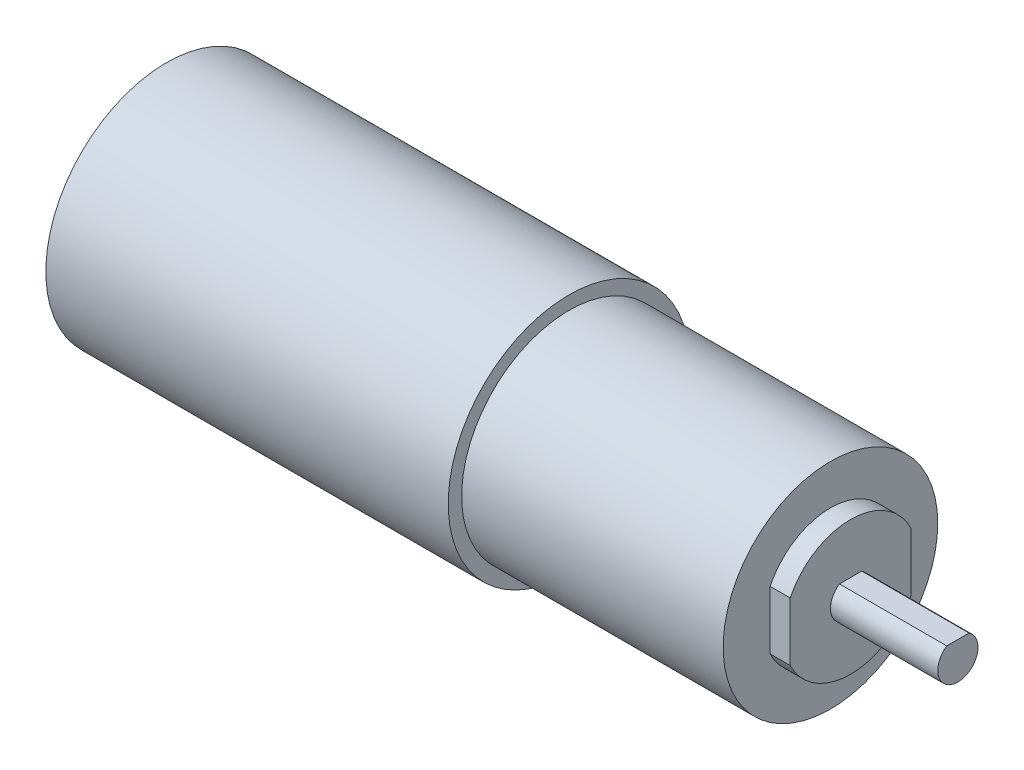
SolidWorks part; units mm, degrees
ref_plane "Front Plane" through (0, 0, 0) normal (0, 0, 1) x (1, 0, 0)
ref_plane "Top Plane" through (0, 0, 0) normal (0, 1, 0) x (1, 0, 0)
ref_plane "Right Plane" through (0, 0, 0) normal (1, 0, 0) x (0, 0, -1)
sketch "Sketch1" plane through (0, 0, 0) normal (1, 0, 0) x (0, 0, -1)
  circle A0 centre (0, 0) radius 18
  dimension "D1" = 36
extrude "Boss-Extrude1" add sketch "Sketch1" along normal blind 60
sketch "Sketch2" plane through (0, 0, 0) normal (-1, 0, 0) x (0, 0, 1)
  circle A0 centre (0, 0) radius 8
  dimension "D1" = 16
extrude "Boss-Extrude2" add sketch "Sketch2" along normal blind 3
sketch "Sketch3" plane through (60, 0, 0) normal (1, 0, 0) x (0, 0, -1)
  circle A0 centre (0, 0) radius 16
  dimension "D1" = 32
extrude "Boss-Extrude3" add sketch "Sketch3" along normal blind 39
sketch "Sketch4" plane through (99, 0, 0) normal (1, 0, 0) x (0, 0, -1)
  line L0 (9, 4.3589) -> (9, -4.3589)
  line L1 (-9, 4.3589) -> (-9, -4.3589)
  arc A0 (-9, -4.3589) -> (9, -4.3589) centre (0, 0) ccw
  arc A1 (9, 4.3589) -> (-9, 4.3589) centre (0, 0) ccw
  dimension "D1" = 20
  dimension "D2" = 9
  dimension "D3" = 9
extrude "Boss-Extrude4" add sketch "Sketch4" along normal blind 3
sketch "Sketch5" plane through (102, 0, 0) normal (1, 0, 0) x (0, 0, -1)
  line L0 (-1.6583, 2.5) -> (1.6583, 2.5)
  arc A0 (-1.6583, 2.5) -> (1.6583, 2.5) centre (0, 0) ccw
  dimension "D1" = 6
  dimension "D2" = 2.5
extrude "Boss-Extrude5" add sketch "Sketch5" along normal blind 16
